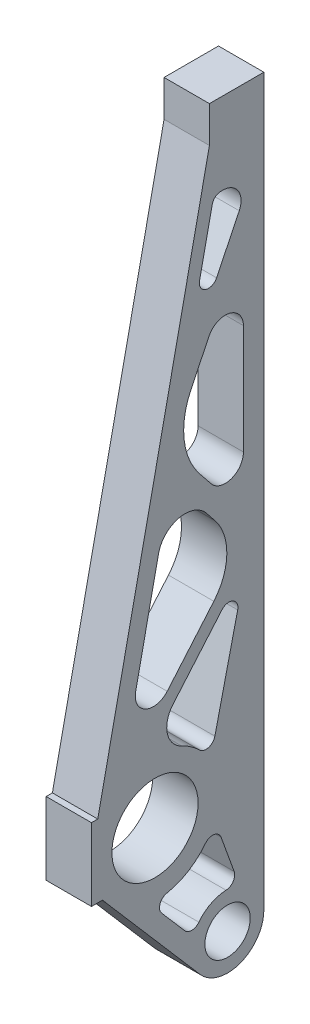
SolidWorks part; units mm, degrees
other "Static 1"
other "Static 2"
other "Static 3 1875"
other "Static 4"
other "Brake Pedal Static 2D FEA"
material "6061-T6 (SS)"
ref_plane "Front Plane" through (0, 0, 0) normal (0, 0, 1) x (1, 0, 0)
ref_plane "Top Plane" through (0, 0, 0) normal (0, 1, 0) x (1, 0, 0)
ref_plane "Right Plane" through (0, 0, 0) normal (1, 0, 0) x (0, 0, -1)
sketch "Sketch1" plane through (0, 0, 0) normal (1, 0, 0) x (0, 0, -1)
  line L0 (0, 0) -> (-25.4, 50.8) construction
  line L1 (-25.4, 50.8) -> (0, 228.6) construction
  line L2 (0, 196.85) -> (0, 228.6) construction
  line L3 (-41.3795, 40.429) -> (-10.653, -6.914)
  line L5 (12.6934, -0.409) -> (19.05, 196.85)
  line L10 (0, 228.6) -> (19.05, 228.6)
  line L14 (0, 196.85) -> (19.05, 196.85)
  line L15 (19.05, 228.6) -> (19.05, 196.85)
  line L16 (0, 228.6) -> (-42.55, 59.0933)
  line L17 (14.4597, 101.8932) -> (-17.6679, 151.6958) construction
  line L18 (17.5196, 196.85) -> (-17.6679, 151.6958) construction
  line L19 (-4.6965, 196.85) -> (-33.4987, 82.1103)
  line L20 (9.8527, 10.0173) -> (15.8734, 196.85)
  line L21 (9.5201, -0.3068) -> (15.8766, 196.9523) construction
  line L24 (520.912, 24.2796) -> (495.512, 68.2737) construction
  line L25 (3.0795, 227.827) -> (-39.4706, 58.3203) construction
  line L27 (17.5196, 196.85) -> (11.3592, 5.6796) construction
  line L28 (-39.891, 63.1658) -> (0, 222.0797) construction
  line L29 (-7.5155, 57.361) -> (11.923, 4.374)
  line L30 (0, 196.85) -> (-4.6965, 196.85)
  line L31 (15.0152, 198.8016) -> (-13.3407, 162.4141)
  line L32 (0, 196.85) -> (0, 0) construction
  line L33 (20.024, 194.8984) -> (-13.7778, 151.5225)
  line L34 (13.0715, 109.9021) -> (-13.7778, 151.5225)
  line L35 (-23.5385, 75.4778) -> (11.1473, 101.3996) construction
  line L36 (-7.8393, 43.4168) -> (12.4964, 92.0542)
  line L37 (17.1277, 103.6144) -> (-13.7778, 151.5225) construction
  line L38 (14.4597, 101.8932) -> (-35.616, 64.47) construction
  line L39 (14.4597, 101.8932) -> (-9.6552, 44.217) construction
  line L40 (11.7917, 100.1721) -> (-21.5581, 151.8691) construction
  line L41 (15.0152, 198.8016) -> (-21.5581, 151.8691) construction
  line L42 (11.1473, 101.3996) -> (-17.5068, 145.8176)
  line L43 (-33.4987, 82.1103) -> (-37.7085, 65.3397)
  line L44 (514.562, 265.5796) -> (495.512, 68.2737) construction
  line L45 (514.562, 252.8796) -> (514.562, 278.2796) construction
  line L46 (514.562, 265.5796) -> (473.5604, 71.8921) construction
  line L47 (478.6895, 53.7494) -> (511.2992, 15.98)
  line L48 (514.562, 278.2796) -> (533.612, 278.2796)
  line L49 (514.562, 252.8796) -> (533.612, 252.8796) construction
  line L50 (533.612, 278.2796) -> (533.612, 252.8796)
  line L51 (-42.4656, 50.8) -> (-40.4812, 50.8)
  line L52 (530.437, 138.5796) -> (497.9096, 179.25) construction
  line L53 (533.612, 252.8796) -> (495.0296, 173.3105) construction
  line L54 (533.612, 252.8796) -> (533.612, 24.2796)
  line L55 (473.287, 68.2737) -> (473.287, 55.5737)
  line L56 (473.287, 55.5737) -> (477.273, 55.5737)
  line L57 (473.287, 68.2737) -> (473.287, 80.9737)
  line L58 (473.287, 80.9737) -> (475.4829, 80.9737)
  line L59 (516.4916, 150.9329) -> (513.4924, 154.6829)
  line L60 (516.1087, 126.6725) -> (499.7922, 107.5415)
  line L61 (514.562, 252.8796) -> (520.912, 24.2796) construction
  line L62 (496.7353, 150.7063) -> (488.7484, 112.9772)
  line L63 (526.3195, 138.6446) -> (495.4301, 177.2669) construction
  line L64 (511.6264, 244.0468) -> (480.6771, 97.845) construction
  line L65 (515.1592, 162.7655) -> (511.1055, 167.834)
  line L66 (530.437, 138.5796) -> (473.5604, 71.8921) construction
  line L67 (514.4045, 207.8099) -> (508.0868, 194.7807)
  line L68 (518.6427, 249.7046) -> (519.2898, 249.7046)
  line L69 (535.7546, 251.8407) -> (500.0523, 178.2111) construction
  line L70 (526.4682, 205.0394) -> (526.4682, 166.7316)
  line L71 (514.562, 249.7046) -> (533.612, 249.7046) construction
  line L72 (525.0036, 240.5841) -> (517.0712, 224.2249)
  line L73 (515.5365, 247.1872) -> (511.1081, 226.2678)
  line L74 (530.437, 219.1065) -> (530.437, 75.3167) construction
  line L75 (532.9165, 140.5627) -> (500.3892, 181.2331) construction
  line L76 (526.3195, 138.6446) -> (465.7409, 67.6164) construction
  line L78 (526.4682, 243.844) -> (526.4682, 166.7316)
  line L79 (524.4524, 119.8778) -> (516.4723, 85.6062)
  line L80 (526.4682, 252.8796) -> (526.4682, 24.2796) construction
  line L81 (518.9444, 122.6582) -> (501.7851, 102.539)
  line L82 (-21.6378, 72.9345) -> (13.0479, 98.8563)
  line L83 (12.995, 102.5056) -> (-11.1198, 44.8294)
  line L84 (514.562, 265.5796) -> (514.562, 278.2796)
  line L85 (497.8713, 41.2493) -> (505.9407, 31.9031)
  line L86 (473.7688, 72.8765) -> (514.562, 265.5796)
  line L87 (523.2226, 41.2207) -> (518.6409, 53.8815)
  line L88 (530.437, 138.5796) -> (514.4793, 70.0468) construction
  line L89 (514.4793, 70.0468) -> (531.1897, 23.87) construction
  line L90 (530.437, 138.5796) -> (469.3061, 66.9039) construction
  line L91 (496.7353, 150.7063) -> (509.1191, 209.2065) construction
  line L92 (533.612, 252.8796) -> (497.9096, 179.25) construction
  circle A0 centre (0, 0) radius 6.35
  circle A1 centre (0, 0) radius 12.7
  circle A2 centre (-25.4, 50.8) radius 15.0812 construction
  circle A3 centre (-25.4, 50.8) radius 19.05
  circle A12 centre (-25.4, 50.8) radius 17.0656 construction
  arc A16 (-33.9601, 65.5635) -> (-34.0265, 65.6579) centre (-35.616, 64.47) ccw
  circle A17 centre (14.4597, 101.8932) radius 3.175 construction
  arc A21 (-11.486, 44.9824) -> (-11.5002, 44.9474) centre (-9.6552, 44.217) ccw
  arc A22 (-7.8393, 43.4168) -> (-7.8244, 43.4515) centre (-9.6552, 44.217) ccw
  arc A23 (-23.5385, 75.4778) -> (-33.4987, 82.1103) centre (-27.3398, 80.5643) cw
  circle A29 centre (530.437, 138.5796) radius 1.5875 construction
  circle A32 centre (520.912, 24.2796) radius 7.9375
  circle A35 centre (-25.4, 50.8) radius 18.2562
  circle A36 centre (-25.4, 50.8) radius 20.2406
  circle A37 centre (495.512, 68.2737) radius 15.0813
  circle A38 centre (-25.4, 50.8) radius 9.525
  circle A39 centre (-25.4, 50.8) radius 11.5094
  arc A42 (511.2992, 15.98) -> (533.612, 24.2796) centre (520.912, 24.2796) ccw
  arc A45 (518.6427, 249.7046) -> (515.5365, 247.1872) centre (518.6427, 246.5296) ccw
  arc A47 (504.8667, 88.4341) -> (501.7851, 102.539) centre (508.6821, 96.6567) cw
  arc A48 (465.7409, 67.6164) -> (467.1418, 63.7881) centre (493.4482, 75.5852) ccw construction
  arc A49 (469.3061, 66.9039) -> (470.0388, 65.0873) centre (493.4482, 75.5852) ccw construction
  arc A50 (517.0712, 224.2249) -> (511.1081, 226.2678) centre (514.2143, 225.6102) cw
  arc A52 (526.4682, 205.0394) -> (514.4045, 207.8099) centre (520.1182, 205.0394) ccw
  arc A53 (526.4682, 166.7316) -> (515.1592, 162.7655) centre (520.1182, 166.7316) cw
  arc A54 (511.1055, 167.834) -> (508.0868, 194.7807) centre (530.9417, 183.6986) cw
  arc A55 (513.4924, 154.6829) -> (496.7353, 150.7063) centre (506.0538, 148.7337) ccw
  arc A56 (516.1087, 126.6725) -> (516.4916, 150.9329) centre (501.6144, 139.0344) ccw
  arc A57 (499.7922, 107.5415) -> (488.7484, 112.9772) centre (494.9608, 111.6621) cw
  arc A59 (518.9444, 122.6582) -> (524.4524, 119.8778) centre (521.3601, 120.5979) cw
  arc A61 (473.7688, 72.8765) -> (478.6895, 53.7494) centre (495.512, 68.2737) ccw
  arc A62 (504.8667, 88.4341) -> (511.1465, 84.0697) centre (495.512, 68.2737) cw
  arc A63 (499.6792, 46.4429) -> (513.1375, 54.7352) centre (495.512, 68.2737) ccw
  arc A64 (510.8575, 32.0383) -> (520.3721, 36.9681) centre (520.912, 24.2796) cw
  circle A68 centre (520.912, 24.2796) radius 9.525 construction
  circle A69 centre (495.512, 68.2737) radius 19.05 construction
  circle A70 centre (520.912, 24.2796) radius 50.8 construction
  arc A72 (516.4723, 85.6062) -> (511.1465, 84.0697) centre (513.38, 86.3262) cw
  arc A73 (520.3721, 36.9681) -> (523.2226, 41.2207) centre (520.2371, 40.1403) ccw
  arc A74 (505.9407, 31.9031) -> (510.8575, 32.0383) centre (508.3439, 33.978) ccw
  arc A75 (499.6792, 46.4429) -> (497.8713, 41.2493) centre (500.2745, 43.3242) ccw
  arc A76 (513.1375, 54.7352) -> (518.6409, 53.8815) centre (515.6554, 52.8011) cw
  arc A77 (533.612, 252.8696) -> (533.612, 252.8896) centre (533.612, 252.8796) ccw
  arc A78 (519.2898, 249.7046) -> (525.0036, 240.5841) centre (519.2898, 243.3546) cw
  point P17 (-42.4656, 50.8)
  point P66 (-13.98, 146.6506)
  dimension "D1" = 30.1625
  dimension "D2" = 38.1
  dimension "D3" = 12.7
  dimension "D4" = 25.4
  dimension "D8" = 19.05
  dimension "D13" = 3.175
  dimension "D14" = 3.175
  dimension "D22" = 52.8584
  dimension "D23" = 6.35
  dimension "D24" = 3.175
  dimension "D25" = 25.4
  dimension "D26" = 22.225
  dimension "D27" = 3.175
  dimension "D28" = 30.1625
  dimension "D29" = 36.5125
  dimension "D10" = 34.1313
  dimension "D15" = 6.35
  dimension "D19" = 3.175
  dimension "D20" = 15.875
  dimension "D30" = 25.4
  dimension "D31" = 19.05
  dimension "D38" = 2.3813
  dimension "D35" = 3.175
  dimension "D40" = 1.5875
  dimension "D46" = 12.7
  dimension "D47" = 1.5875
  dimension "D49" = 38.1
  dimension "D50" = 6.35
  dimension "D53" = 12.7
  dimension "D54" = 19.05
  dimension "D60" = 3.175
  dimension "D61" = 3.175
  dimension "D57" = 114.3
  dimension "D58" = 19.05
  dimension "D59" = 25.4
  dimension "D33" = 50.8
  dimension "D62" = 254
  dimension "D63" = 6.35
  dimension "D64" = 6.35
  dimension "D65" = 9.525
  dimension "D34" = 0.01
  dimension "D5" = 25.4
  dimension "D6" = 228.6
  dimension "D7" = 50.8
  dimension "D9" = 31.75
  dimension "D11" = 3.175
  dimension "D12" = 3.175
  dimension "D16" = 56.7961
  dimension "D17" = 1.5875
  dimension "D18" = 96.2136
  dimension "D21" = 69.5855
  dimension "D32" = 25.4
  dimension "D36" = 3.175
  dimension "D37" = 3.175
  dimension "D43" = 4.7625
  dimension "D44" = 4.7625
  dimension "D45" = 2.3813
  dimension "D41" = 7.1437
  dimension "D48" = 3.175
  dimension "D51" = 6.35
  dimension "D52" = 1.5875
  dimension "D55" = 4.7625
  dimension "D56" = 3.175
  dimension "D39" = 3.175
  dimension "D42" = 1.5875
extrude "Boss-Extrude1" add sketch "Sketch1" along normal mid plane 15.875
sketch "Sketch2" plane through (0, 0, -533.612) normal (0, 0, -1) x (-1, 0, 0)
  line L1 (-7.9375, 278.2796) -> (7.9375, 278.2796) construction
  line L2 (0, 278.2796) -> (0, 248.165) construction
  point P0 (0, 271.9296)
  point P1 (0, 259.2296)
  dimension "D2" = 6.35
  dimension "D3" = 12.7
hole_wizard "Tap Drill for 1/4-28 Tap1" positions "3DSketch1" profile "Sketch3" hole size "1/4-28" standard "ANSI Inch"
sketch3d "3DSketch1"
  point P0 (0, 271.9296, -533.612)
  point P3 (0, 259.2296, -533.612)
sketch "Sketch3" plane through (0, 271.9296, -533.612) normal (1, 0, 0) x (0, 1, 0)
  line L0 (0, 0) -> (0, 15.875)
  line L1 (0, 15.875) -> (2.7051, 14.2496)
  line L2 (2.7051, 14.2496) -> (2.7051, 0)
  line L5 (2.7051, 0) -> (0, 0)
  line L10 (0, 15.875) -> (-2.7051, 14.2496) construction
  line L11 (0, -6.35) -> (0, 107.95) construction
  dimension "Hole Dia." = 5.4102
  dimension "Hole Depth" = 15.875
  dimension "Drill Angle" = 118
